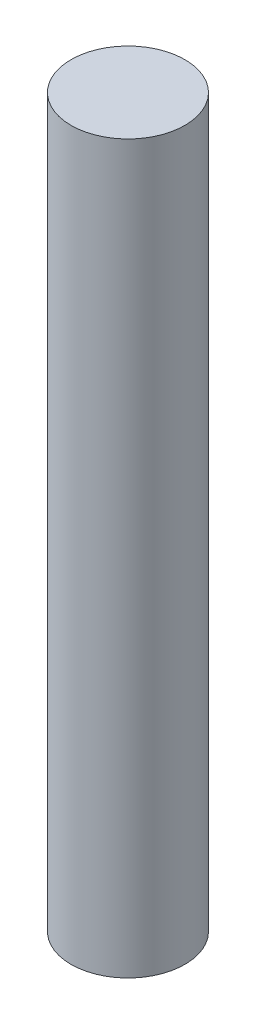
SolidWorks part; units mm, degrees
ref_plane "Front Plane" through (0, 0, 0) normal (0, 0, 1) x (1, 0, 0)
ref_plane "Top Plane" through (0, 0, 0) normal (0, 1, 0) x (1, 0, 0)
ref_plane "Right Plane" through (0, 0, 0) normal (1, 0, 0) x (0, 0, -1)
sketch "Sketch1" plane through (0, 0, 0) normal (0, 1, 0) x (1, 0, 0)
  circle A0 centre (0, 0) radius 14.5
  dimension "D1" = 29
extrude "Boss-Extrude1" add sketch "Sketch1" along normal blind 185 contours A0
equation "\"MotorDiam\"= 29'Outer diamiter of the motor tube"
equation "\"MotorLength\"= 185'End to end length of the motor"
